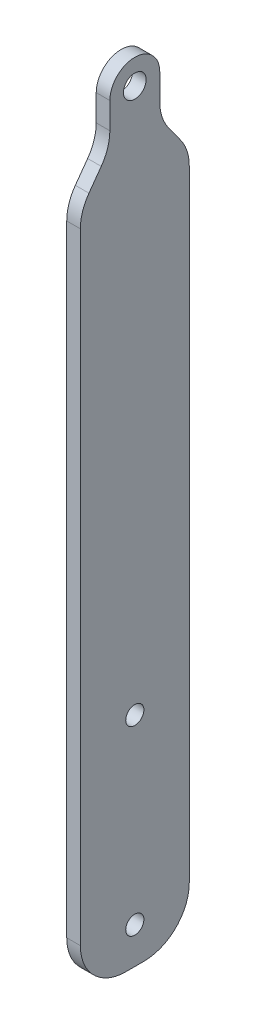
SolidWorks part; units mm, degrees
ref_plane "Front Plane" through (0, 0, 0) normal (0, 0, 1) x (1, 0, 0)
ref_plane "Top Plane" through (0, 0, 0) normal (0, 1, 0) x (1, 0, 0)
ref_plane "Right Plane" through (0, 0, 0) normal (1, 0, 0) x (0, 0, -1)
sketch "Sketch1" plane through (18.3, 0, 0) normal (1, 0, 0) x (0, 0, -1)
  line L2 (61.5, -7.3539) -> (61.5, -16.3539)
  line L3 (72.5, -7.3539) -> (72.5, -16.3539)
  line L5 (61.5, -16.3539) -> (55, -25.3539)
  line L6 (72.5, -16.3539) -> (79, -25.3539)
  line L7 (79, -25.3539) -> (79, -175.3539)
  line L8 (79, -175.3539) -> (55, -175.3539)
  line L9 (55, -175.3539) -> (55, -25.3539)
  line L10 (55, -25.3539) -> (79, -25.3539) construction
  line L11 (67, -25.3539) -> (67, -16.3539) construction
  line L12 (61.5, -16.3539) -> (72.5, -16.3539) construction
  circle A0 centre (67, -7.3539) radius 2.5 construction
  circle A1 centre (67, -7.3539) radius 2.5
  arc A2 (61.5, -7.3539) -> (72.5, -7.3539) centre (67, -7.3539) cw
  point P14 (67, -16.3539)
  dimension "D1" = 5.5
  dimension "D2" = 9
  dimension "D3" = 9
  dimension "D4" = 24
  dimension "D5" = 150
extrude "Boss-Extrude1" add sketch "Sketch1" along normal blind 3
sketch "Sketch4" plane through (18.3, 0, 0) normal (-1, 0, 0) x (0, 0, 1)
  line L0 (-67, -175.3539) -> (-67, -25.3539) construction
  line L1 (-55, -175.3539) -> (-79, -175.3539) construction
  line L2 (-79, -25.3539) -> (-55, -25.3539) construction
  line L3 (-72, -25.3539) -> (-75, -175.3539)
  line L4 (-62, -25.3539) -> (-59, -175.3539)
  line L5 (-75, -175.3539) -> (-59, -175.3539)
  arc A0 (-72, -25.3539) -> (-62, -25.3539) centre (-67, -25.3539) cw
  dimension "D1" = 5
  dimension "D2" = 16
extrude "Boss-Extrude2" add sketch "Sketch4" along normal blind 2
fillet "Fillet4" radius 10 6 edges at (19.8, -175.3539, -55) (19.8, -175.3539, -79) (19.8, -25.3539, -55) (19.8, -16.3539, -61.5) (19.8, -25.3539, -79) (19.8, -16.3539, -72.5)
sketch "Sketch5" plane through (16.3, 0, 0) normal (-1, 0, 0) x (0, 0, 1)
  line L0 (-67, -175.3539) -> (-67, -127.3539) construction
  line L1 (-69, -175.3539) -> (-65, -175.3539) construction
  circle A0 centre (-67, -127.3539) radius 2
  circle A1 centre (-67, -167.3539) radius 2
  dimension "D1" = 4
  dimension "D2" = 40
  dimension "D3" = 8
extrude "Cut-Extrude1" cut sketch "Sketch5" against normal through all
